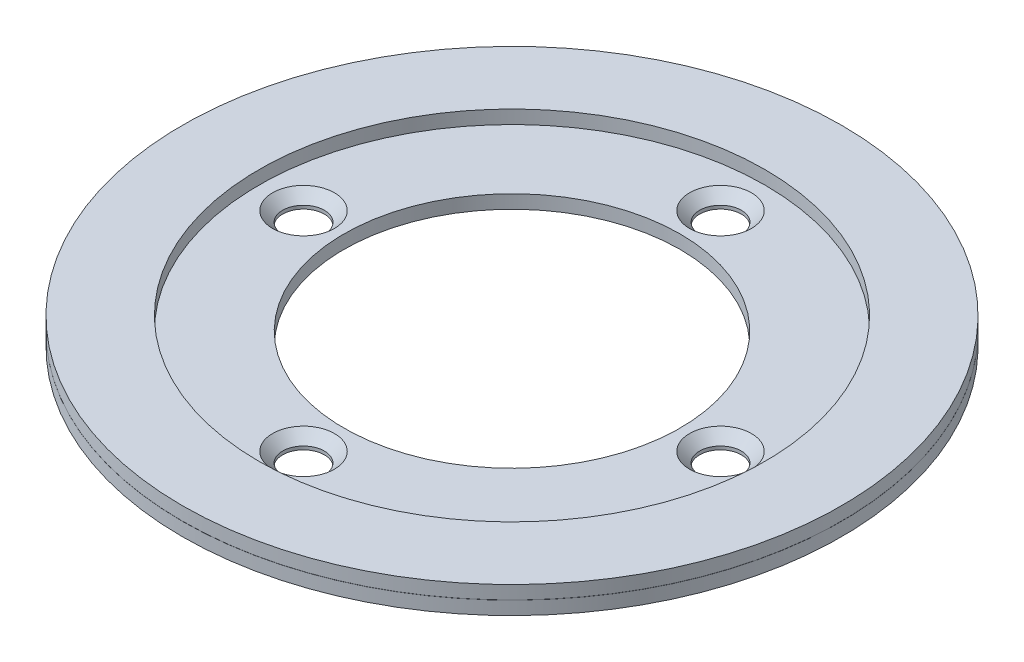
SolidWorks part; units mm, degrees
ref_plane "Front Plane" through (0, 0, 0) normal (0, 0, 1) x (1, 0, 0)
ref_plane "Top Plane" through (0, 0, 0) normal (0, 1, 0) x (1, 0, 0)
ref_plane "Right Plane" through (0, 0, 0) normal (1, 0, 0) x (0, 0, -1)
sketch "Sketch1" plane through (0, 0, 0) normal (0, 0, 1) x (1, 0, 0)
  line L0 (0, 0) -> (0, 15.4131) construction
  line L1 (-24.5, 0) -> (-12.5, 0)
  line L2 (-24.5, 0) -> (-24.5, 0.995)
  line L3 (-24.5, 2) -> (-18.8, 2)
  line L4 (-12.5, 0) -> (-12.5, 1)
  line L5 (-24.5, 1.005) -> (-24.5, 2)
  line L6 (-24.5, 1.005) -> (-24, 1.005)
  line L8 (-12.5, 1) -> (-18.8, 1)
  line L9 (-18.8, 2) -> (-18.8, 1)
  line L10 (-24.5, 0.995) -> (-24, 0.995)
  line L11 (-24, 1.005) -> (-24, 0.995)
  dimension "D1" = 49
  dimension "D2" = 25
  dimension "D3" = 2
  dimension "D4" = 37.6
  dimension "D5" = 0.5
  dimension "D6" = 0.01
revolve "Revolve1" add sketch "Sketch1" angle 360 about L0
hole_wizard "CSK for M2.5 Countersunk Flat Head Screw1" positions "Sketch3" profile "Sketch2" countersink size "M2.5" standard "DIN" end condition through all
sketch "Sketch3" plane through (0, 1, 0) normal (0, 1, 0) x (1, 0, 0)
  circle A0 centre (0, 0) radius 15.5 construction
  point P0 (0, 15.5)
  point P2 (-15.5, 0)
  point P4 (0, -15.5)
  point P6 (15.5, 0)
  dimension "D1" = 31
sketch "Sketch2" plane through (0, 1, -15.5) normal (1, 0, 0) x (0, 0, 1)
  line L0 (0, 0) -> (0, 1)
  line L1 (0, 1) -> (1.55, 1)
  line L2 (1.55, 1) -> (1.55, 0.75)
  line L3 (1.55, 0.75) -> (2.3, 0)
  line L5 (2.3, 0) -> (0, 0)
  line L6 (-1.55, 0.75) -> (-2.3, 0) construction
  line L11 (0, -6.35) -> (0, 107.95) construction
  dimension "Thru Hole Dia." = 3.1
  dimension "Thru Hole Depth" = 1
  dimension "Near C'Sink Dia." = 4.6
  dimension "Near C'Sink Angle" = 90
